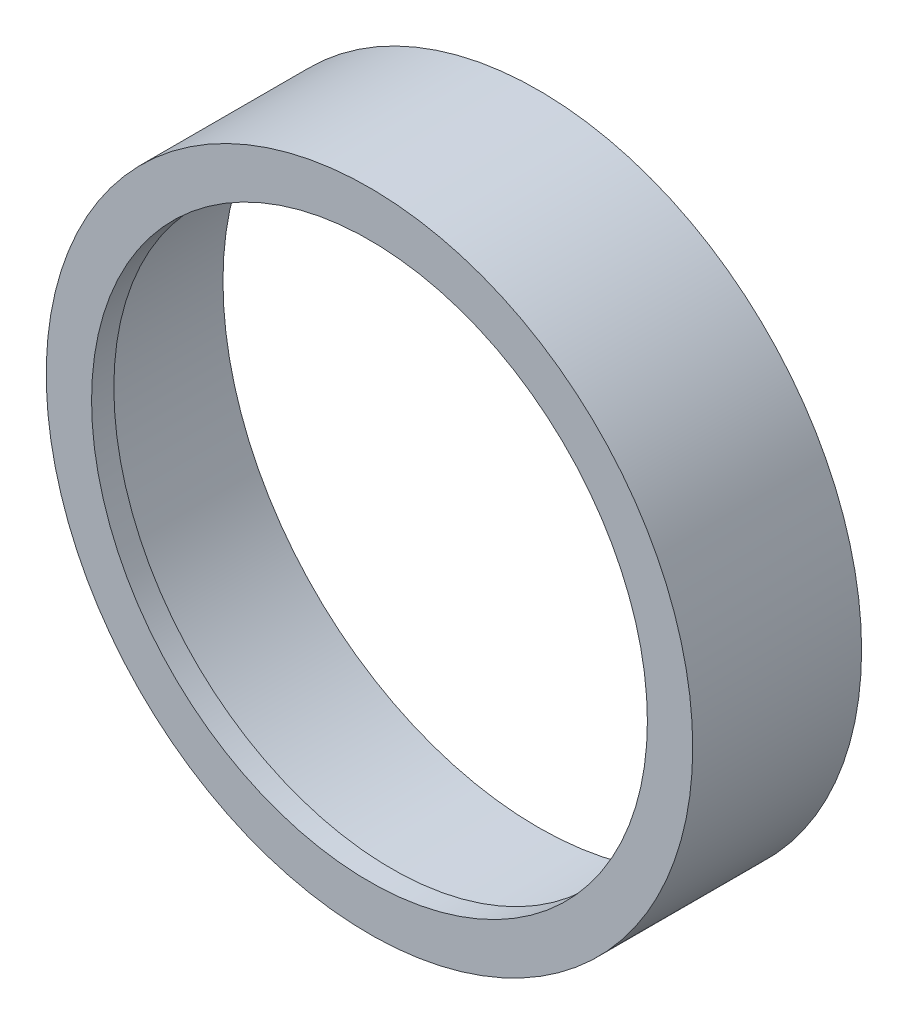
SolidWorks part; units mm, degrees
ref_plane "Front Plane" through (0, 0, 0) normal (0, 0, 1) x (1, 0, 0)
ref_plane "Top Plane" through (0, 0, 0) normal (0, 1, 0) x (1, 0, 0)
ref_plane "Right Plane" through (0, 0, 0) normal (1, 0, 0) x (0, 0, -1)
sketch "Sketch1" plane through (0, 0, 0) normal (0, 0, 1) x (1, 0, 0)
  circle A0 centre (0, 0) radius 24.81
  dimension "D1" = 49.62
extrude "Boss-Extrude1" add sketch "Sketch1" along normal blind 12.96
sketch "Sketch3" plane through (0, 0, 0) normal (0, 0, -1) x (-1, 0, 0)
  circle A0 centre (0, 0) radius 24.205
  dimension "D1" = 48.41
extrude "Cut-Extrude2" cut sketch "Sketch3" against normal blind 11.25
sketch "Sketch4" plane through (0, 0, 12.96) normal (0, 0, 1) x (1, 0, 0)
  circle A1 centre (0, 0) radius 21.33
  dimension "D1" = 42.66
extrude "Cut-Extrude3" cut sketch "Sketch4" against normal blind 11.25
equation "\"ODia\"= 49.62mm"
equation "\"IDia\"= 48.41mm"
equation "\"InnerLength\"= 11.25mm"
equation "\"OutterLength\"= 12.96mm"
equation "\"D1@Sketch1\"=\"ODia\""
equation "\"D1@Boss-Extrude1\"=\"OutterLength\""
equation "\"D1@Sketch3\"=\"IDia\""
equation "\"LipDia\"= 42.66mm"
